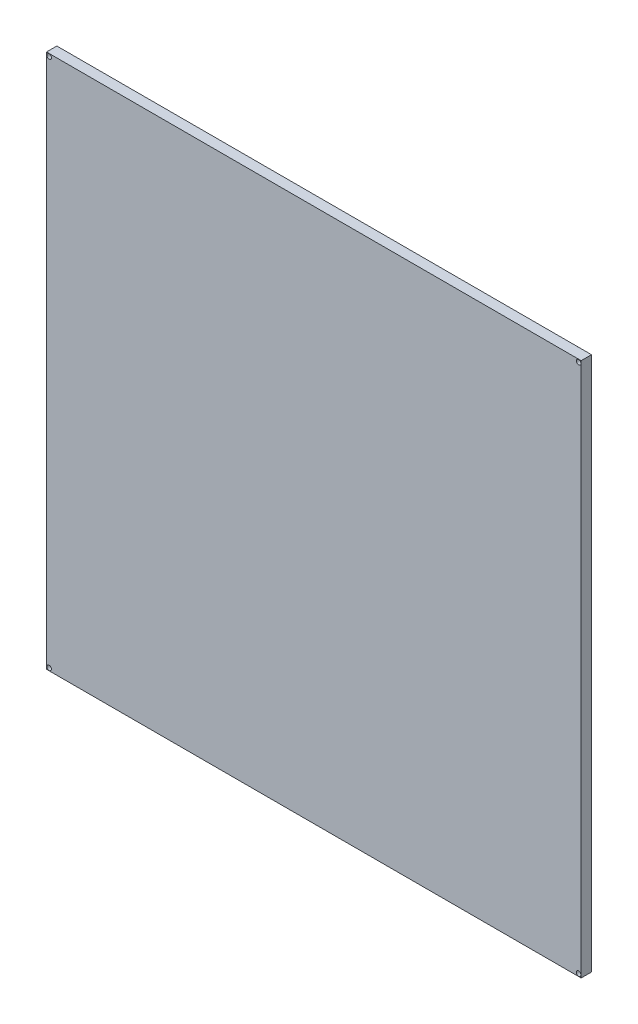
SolidWorks part; units mm, degrees
ref_plane "Front Plane" through (0, 0, 0) normal (0, 0, 1) x (1, 0, 0)
ref_plane "Top Plane" through (0, 0, 0) normal (0, 1, 0) x (1, 0, 0)
ref_plane "Right Plane" through (0, 0, 0) normal (1, 0, 0) x (0, 0, -1)
sketch "Sketch1" plane through (0, 0, 0) normal (0, 0, 1) x (1, 0, 0)
  line L1 (-13.1482, 24.0497) -> (38.6518, 24.0497)
  line L2 (-13.1482, 24.0497) -> (-13.1482, -27.7503)
  line L3 (-13.1482, -27.7503) -> (38.6518, -27.7503)
  line L4 (38.6518, 24.0497) -> (38.6518, -27.7503)
  dimension "D1" = 51.8
  dimension "D2" = 51.8
extrude "Boss-Extrude1" add sketch "Sketch1" along normal blind 1
sketch "Sketch2" plane through (0, 0, 0) normal (0, 0, -1) x (-1, 0, 0)
  circle A0 centre (-38.4048, 23.801) radius 0.225
  circle A1 centre (-38.4048, -27.5016) radius 0.225
  circle A2 centre (12.8944, -27.5016) radius 0.225
  circle A3 centre (12.8944, 23.801) radius 0.225
  dimension "D4" = 0.45
extrude "Cut-Extrude1" cut sketch "Sketch2" against normal through all
